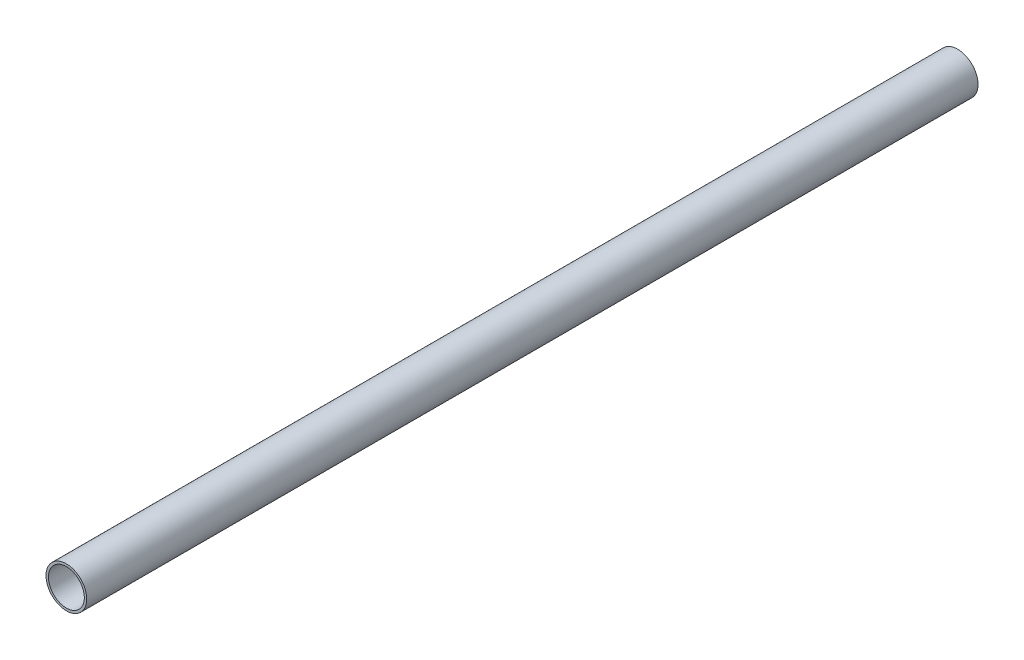
SolidWorks part; units mm, degrees
ref_plane "Front Plane" through (0, 0, 0) normal (0, 0, 1) x (1, 0, 0)
ref_plane "Top Plane" through (0, 0, 0) normal (0, 1, 0) x (1, 0, 0)
ref_plane "Right Plane" through (0, 0, 0) normal (1, 0, 0) x (0, 0, -1)
sketch "Sketch1" plane through (0, 0, 0) normal (0, 0, 1) x (1, 0, 0)
  circle A0 centre (0, 0) radius 17
  dimension "D1" = 34
extrude "Extrude1" add sketch "Sketch1" along normal mid plane 744
shell "Shell1" thickness 2
